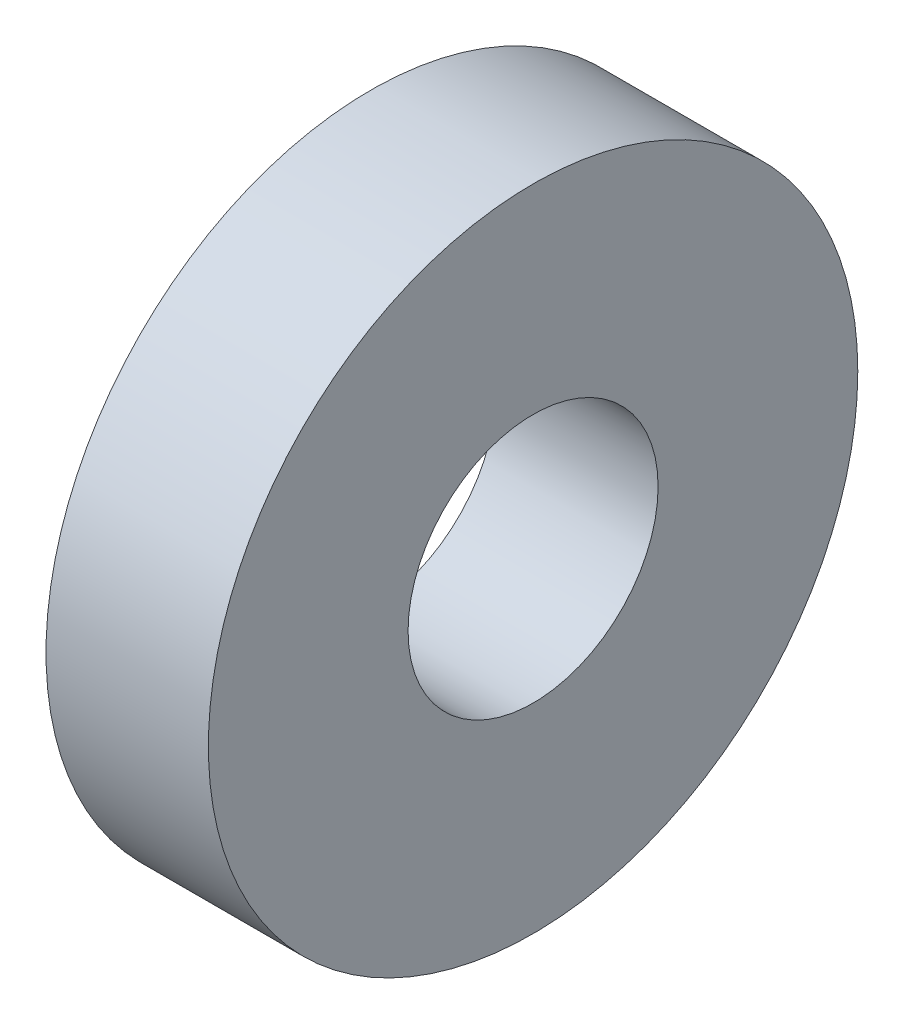
SolidWorks part; units mm, degrees
material "1060 Alloy"
ref_plane "Front Plane" through (0, 0, 0) normal (0, 0, 1) x (1, 0, 0)
ref_plane "Top Plane" through (0, 0, 0) normal (0, 1, 0) x (1, 0, 0)
ref_plane "Right Plane" through (0, 0, 0) normal (1, 0, 0) x (0, 0, -1)
sketch "Sketch1" plane through (0, 0, 0) normal (1, 0, 0) x (0, 0, -1)
  circle A0 centre (0, 0) radius 4.8895
  circle A1 centre (0, 0) radius 12.7
  dimension "D1" = 25.4
  dimension "D2" = 9.779
extrude "Boss-Extrude1" add sketch "Sketch1" along normal blind 6.35
